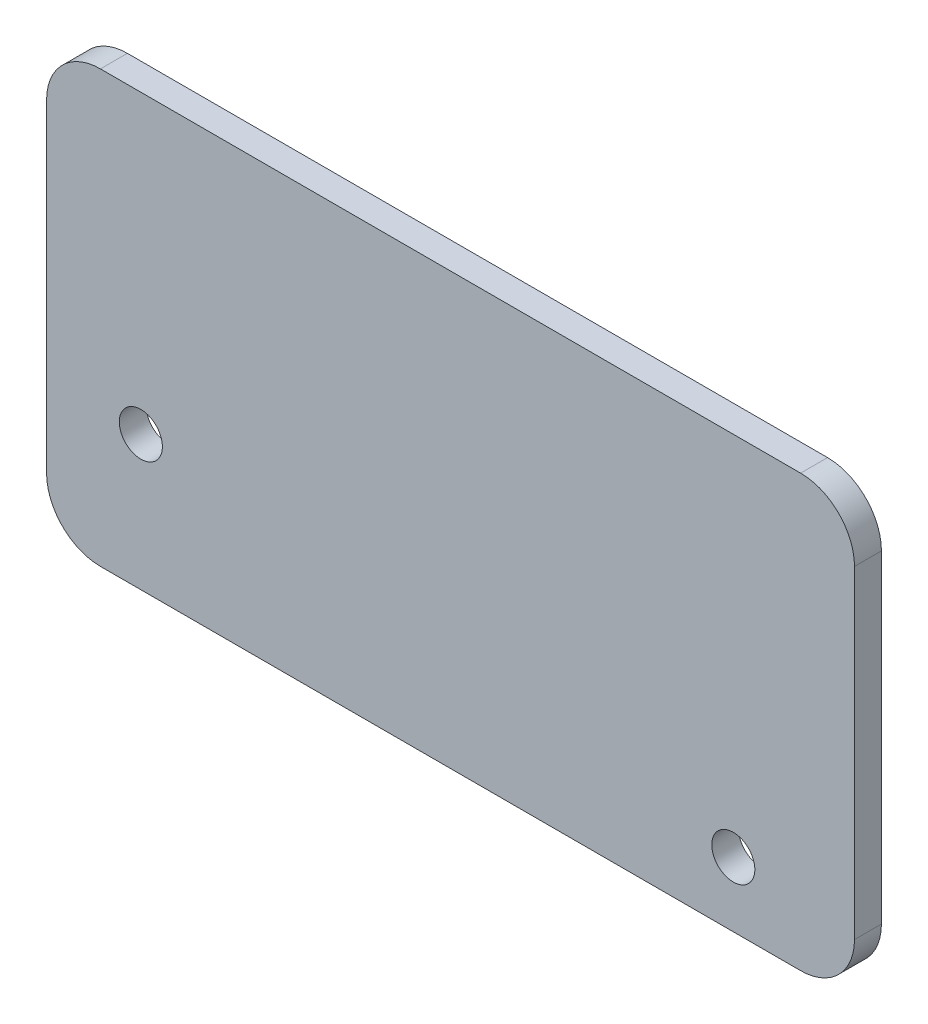
SolidWorks part; units mm, degrees
ref_plane "Front Plane" through (0, 0, 0) normal (0, 0, 1) x (1, 0, 0)
ref_plane "Top Plane" through (0, 0, 0) normal (0, 1, 0) x (1, 0, 0)
ref_plane "Right Plane" through (0, 0, 0) normal (1, 0, 0) x (0, 0, -1)
sketch "Sketch1" plane through (0, 0, 0) normal (0, 0, 1) x (1, 0, 0)
  line L1 (-65, 40) -> (65, 40)
  line L2 (-75, 30) -> (-75, -30)
  line L3 (-65, -40) -> (65, -40)
  line L4 (75, 30) -> (75, -30)
  line L5 (-75, 40) -> (75, -40) construction
  line L6 (-75, -40) -> (75, 40) construction
  arc A0 (75, 30) -> (65, 40) centre (65, 30) ccw
  arc A1 (65, -40) -> (75, -30) centre (65, -30) ccw
  arc A2 (-75, 30) -> (-65, 40) centre (-65, 30) cw
  arc A3 (-65, -40) -> (-75, -30) centre (-65, -30) cw
  circle A4 centre (52.5, -28) radius 4
  circle A5 centre (-57.5, -15) radius 4
  circle A6 centre (-57.5, -15) radius 4 construction
  point P0 (0, 0)
  dimension "D3" = 10
  dimension "D4" = 10
  dimension "D5" = 10
  dimension "D6" = 10
  dimension "D7" = 8
  dimension "D8" = 8
  dimension "D1" = 150
  dimension "D2" = 80
  dimension "D9" = 12
extrude "Boss-Extrude1" add sketch "Sketch1" along normal blind 5
